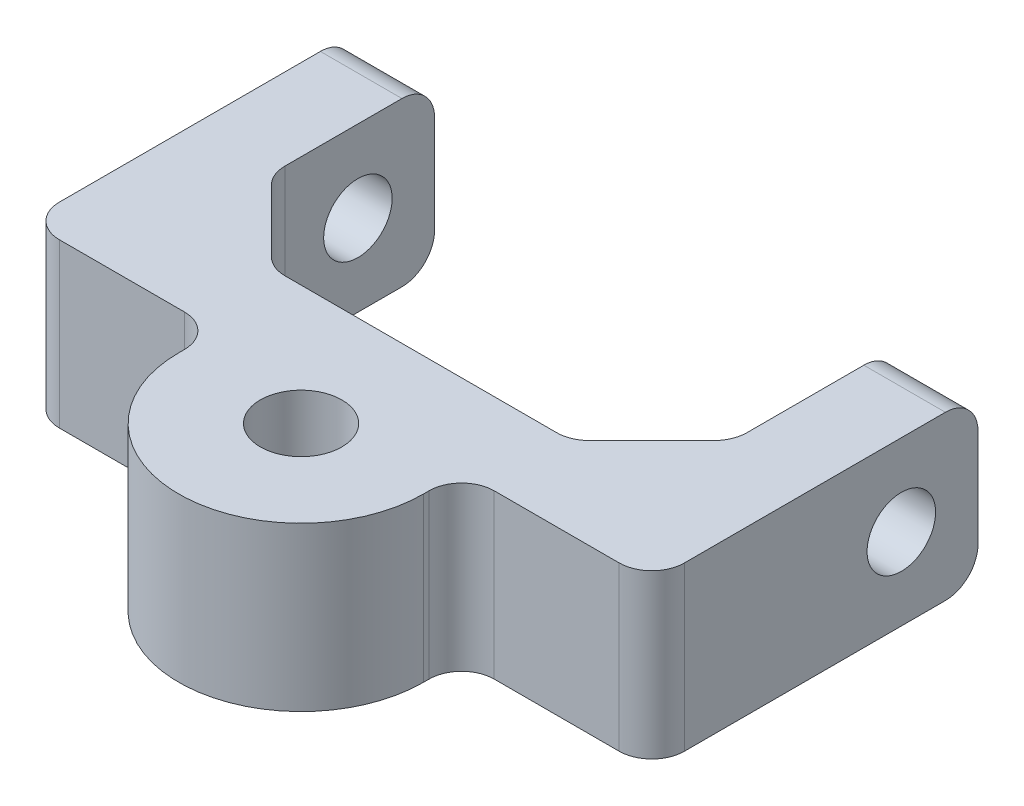
SolidWorks part; units mm, degrees
ref_plane "Front" through (0, 0, 0) normal (0, 0, 1) x (1, 0, 0)
ref_plane "Top" through (0, 0, 0) normal (0, 1, 0) x (1, 0, 0)
ref_plane "Right" through (0, 0, 0) normal (1, 0, 0) x (0, 0, -1)
sketch "Sketch1" plane through (0, 0, 0) normal (0, 1, 0) x (1, 0, 0)
  line L0 (-6.35, -6.35) -> (-6.35, 19.05)
  line L1 (0, 0) -> (35.9664, 0)
  line L2 (0, 0) -> (0, 19.05)
  line L4 (35.9664, 0) -> (35.9664, 19.05)
  line L5 (-6.35, -6.35) -> (42.3164, -6.35)
  line L6 (42.3164, -6.35) -> (42.3164, 19.05)
  line L7 (0, 19.05) -> (-6.35, 19.05)
  line L8 (35.9664, 19.05) -> (42.3164, 19.05)
  point P5 (0, 0)
  dimension "D1" = 19.05
  dimension "D2" = 35.9664
  dimension "D3" = 6.35
extrude "Boss-Extrude1" add sketch "Sketch1" along normal blind 12.7
sketch "Sketch2" plane through (42.3164, 0, 0) normal (1, 0, 0) x (0, 0, -1)
  line L0 (13.081, 6.35) -> (19.05, 6.35) construction
  line L1 (19.05, 12.7) -> (19.05, 0) construction
  circle A0 centre (13.081, 6.35) radius 2.667
  dimension "D1" = 5.334
  dimension "D2" = 5.969
extrude "Cut-Extrude1" cut sketch "Sketch2" against normal through all
sketch "Sketch3" plane through (0, 12.7, 0) normal (0, 1, 0) x (1, 0, 0)
  line L0 (17.9832, 0) -> (17.9832, 6.0248) construction
  line L1 (0, 0) -> (6.35, 0)
  line L2 (0, 0) -> (0, 6.35)
  line L5 (35.9664, 0) -> (0, 0) construction
  line L6 (0, 6.35) -> (6.35, 0)
  line L7 (35.9664, 6.35) -> (29.6164, 0)
  line L8 (35.9664, 0) -> (35.9664, 6.35)
  line L9 (35.9664, 0) -> (29.6164, 0)
  dimension "D1" = 6.35
extrude "Boss-Extrude3" add sketch "Sketch3" against normal up to surface (12.7 mm away) up to face at (17.9832, 0, -7.9375)
sketch "Sketch4" plane through (0, 0, 0) normal (0, -1, 0) x (1, 0, 0)
  line L0 (27.5082, 9.3261) -> (27.5082, 6.35)
  line L1 (-6.35, 6.35) -> (42.3164, 6.35) construction
  line L2 (8.4582, 9.3261) -> (8.4582, 6.35)
  line L3 (27.5082, 6.35) -> (8.4582, 6.35)
  arc A0 (27.5082, 9.3261) -> (8.4582, 9.3261) centre (17.9832, 9.3261) ccw
  dimension "D1" = 19.05
extrude "Boss-Extrude4" add sketch "Sketch4" against normal up to surface (12.7 mm away) up to face at (17.9832, 12.7, -7.62)
sketch "Sketch5" plane through (0, 0, 0) normal (0, -1, 0) x (1, 0, 0)
  circle A0 centre (17.9832, 9.3261) radius 3.175
  dimension "D1" = 6.35
extrude "Cut-Extrude2" cut sketch "Sketch5" against normal up to next
fillet "Fillet1" radius 2.54 4 edges at (-6.35, 6.35, 6.35) (8.4582, 6.35, 6.35) (42.3164, 6.35, 6.35) (27.5082, 6.35, 6.35)
fillet "rr" radius 2.54 4 edges at (0, 6.35, -6.35) (6.35, 6.35, 0) (29.6164, 6.35, 0) (35.9664, 6.35, -6.35)
fillet "Fillet3" radius 2.54 4 edges at (-3.175, 0, -19.05) (-3.175, 12.7, -19.05) (39.1414, 0, -19.05) (39.1414, 12.7, -19.05)
